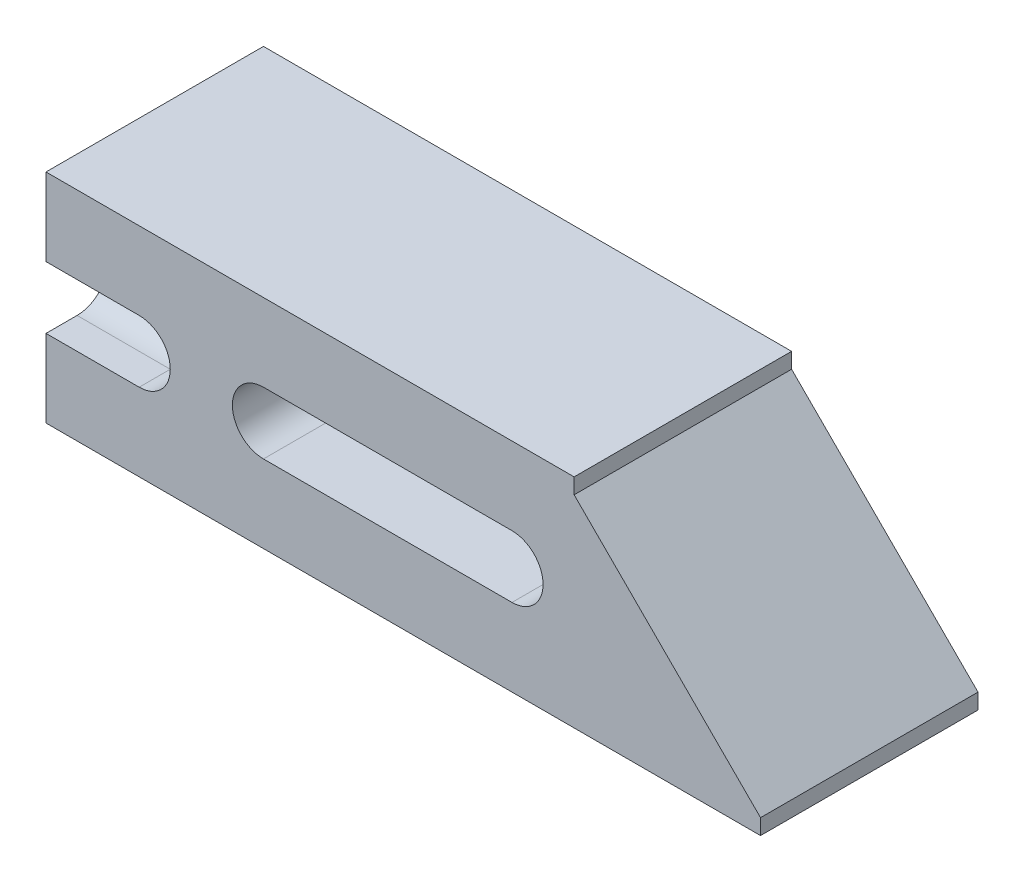
SolidWorks part; units mm, degrees
material "Delrin 2700 NC010, Low Viscosity Acetal Copolymer (SS)"
ref_plane "Front Plane" through (0, 0, 0) normal (0, 0, 1) x (1, 0, 0)
ref_plane "Top Plane" through (0, 0, 0) normal (0, 1, 0) x (1, 0, 0)
ref_plane "Right Plane" through (0, 0, 0) normal (1, 0, 0) x (0, 0, -1)
sketch "Sketch1" plane through (0, 0, 0) normal (0, 0, 1) x (1, 0, 0)
  line L0 (0, 0) -> (0, 22.225)
  line L1 (0, 22.225) -> (53.975, 22.225)
  line L2 (53.975, 22.225) -> (53.975, 20.6375)
  line L3 (53.975, 20.6375) -> (73.025, 1.5875)
  line L4 (73.025, 1.5875) -> (73.025, 0)
  line L5 (73.025, 0) -> (0, 0)
  dimension "D1" = 45
  dimension "D2" = 1.5875
  dimension "D3" = 22.225
  dimension "D4" = 73.025
  dimension "D5" = 19.05
extrude "Boss-Extrude1" add sketch "Sketch1" along normal blind 22.225
sketch "Sketch2" plane through (0, 0, 0) normal (-1, 0, 0) x (0, 0, 1)
  line L0 (22.225, 22.225) -> (0, 0) construction
  circle A0 centre (11.1125, 11.1125) radius 3.5
  dimension "D1" = 7
extrude "Cut-Extrude1" [suppressed] cut sketch "Sketch2" against normal blind 25.4
chamfer "Chamfer1" [suppressed] distance 0.7937 angle 45
thread "Thread1" [suppressed] pitch 1 start angle 0, offset 1.27, length 19.05, pitch 1, diameter 7
ref_plane "Plane1" through (-0.4762, 11.1125, 7.6125) normal (0, -1, 0) x (0, 0, -1)
sketch "Thread Profile1" plane through (-0.4762, 11.1125, 7.6125) normal (0, -1, 0) x (0, 0, -1)
  line L0 (0, 0) -> (0, 1) construction
  line L1 (0, 0) -> (0.5413, 0.3125)
  line L2 (0.5413, 0.3125) -> (0.5413, 0.4375)
  line L3 (0.5413, 0.4375) -> (0, 0.75)
  line L4 (0.5413, 0.375) -> (0, 0.375) construction
  line L11 (0, 0) -> (0, 0.75)
  point P2 (0, 0)
  dimension "Pitch" = 1
  dimension "Profile_Angle" = 60
  dimension "Profile_Land" = 0.125
  dimension "Profile_Height" = 0.5413
sketch "Sketch7" [suppressed] plane through (0, 0, 0) normal (-1, 0, 0) x (0, 0, 1)
  line L0 (7.1438, 11.1125) -> (15.0813, 11.1125) construction
  circle A0 centre (7.1438, 11.1125) radius 2.3813
  circle A1 centre (15.0813, 11.1125) radius 2.3813
  point P0 (11.1125, 11.1125)
  point P5 (11.1125, 11.1125)
  dimension "D2" = 4.7625
  dimension "D1" = 7.9375
extrude "Cut-Extrude2" [suppressed] cut sketch "Sketch7" against normal blind 25.4
sketch "Sketch8" plane through (0, 0, 22.225) normal (0, 0, 1) x (1, 0, 0)
  line L0 (0, 11.1125) -> (50.8, 11.1125) construction
  line L1 (0, 22.225) -> (0, 0) construction
  line L3 (22.225, 14.2875) -> (47.625, 14.2875)
  line L4 (47.625, 7.9375) -> (22.225, 7.9375)
  line L5 (53.975, 20.6375) -> (53.975, 22.225) construction
  arc A0 (47.625, 7.9375) -> (47.625, 14.2875) centre (47.625, 11.1125) ccw
  arc A1 (22.225, 14.2875) -> (22.225, 7.9375) centre (22.225, 11.1125) ccw
  circle A2 centre (9.525, 11.1125) radius 3.175
  dimension "D1" = 6.35
  dimension "D2" = 6.35
  dimension "D5" = 6.35
  dimension "D3" = 25.4
  dimension "D4" = 6.35
  dimension "D6" = 9.525
extrude "Cut-Extrude7" cut sketch "Sketch8" against normal blind 29.21 contours L3 A0 L4 A1 | A2
sketch "Sketch10" plane through (0, 0, 0) normal (-1, 0, 0) x (0, 0, 1)
  line L1 (0, 11.1125) -> (22.225, 11.1125) construction
  line L2 (0, 22.225) -> (0, 0) construction
  line L3 (22.225, 22.225) -> (22.225, 0) construction
  line L4 (3.175, 14.2875) -> (0, 14.2875)
  line L5 (0, 14.2875) -> (0, 7.9375)
  line L6 (0, 7.9375) -> (3.175, 7.9375)
  line L7 (19.05, 7.9375) -> (22.225, 7.9375)
  line L8 (22.225, 7.9375) -> (22.225, 14.2875)
  line L9 (22.225, 14.2875) -> (19.05, 14.2875)
  arc A1 (19.05, 14.2875) -> (19.05, 7.9375) centre (19.05, 11.1125) ccw
  arc A2 (3.175, 7.9375) -> (3.175, 14.2875) centre (3.175, 11.1125) ccw
  dimension "D1" = 6.35
  dimension "D2" = 3.175
  dimension "D3" = 6.35
  dimension "D4" = 3.175
  dimension "D5" = 3.175
extrude "Cut-Extrude8" cut sketch "Sketch10" against normal up to surface (9.525 mm away)
